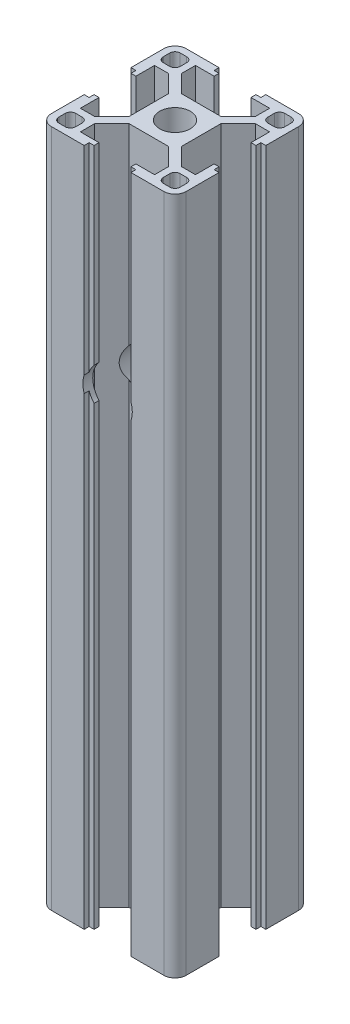
SolidWorks part; units mm, degrees
ref_plane "Front Plane" through (0, 0, 0) normal (0, 0, 1) x (1, 0, 0)
ref_plane "Top Plane" through (0, 0, 0) normal (0, 1, 0) x (1, 0, 0)
ref_plane "Right Plane" through (0, 0, 0) normal (1, 0, 0) x (0, 0, -1)
ref_plane "Plane1" through (0, 100, 0) normal (0, 1, 0) x (1, 0, 0)
sketch "Sketch1" plane through (0, 100, 0) normal (0, 1, 0) x (1, 0, 0)
  line L0 (28.5, -25.9) -> (28.5, -27.35)
  line L1 (27.35, -28.5) -> (25.9, -28.5)
  line L2 (24.75, -27.35) -> (24.75, -25.9)
  line L3 (25.9, -24.75) -> (27.35, -24.75)
  line L4 (1.5, -27.35) -> (1.5, -25.9)
  line L5 (2.65, -24.75) -> (4.1, -24.75)
  line L6 (5.25, -25.9) -> (5.25, -27.35)
  line L7 (4.1, -28.5) -> (2.65, -28.5)
  line L8 (2.65, -1.5) -> (4.1, -1.5)
  line L9 (5.25, -2.65) -> (5.25, -4.1)
  line L10 (4.1, -5.25) -> (2.65, -5.25)
  line L11 (1.5, -4.1) -> (1.5, -2.65)
  line L12 (28.5, -2.65) -> (28.5, -4.1)
  line L13 (27.35, -5.25) -> (25.9, -5.25)
  line L14 (24.75, -4.1) -> (24.75, -2.65)
  line L15 (25.9, -1.5) -> (27.35, -1.5)
  line L16 (27.5, 0) -> (20.2, 0)
  line L17 (20.2, 0) -> (20.2, -1.1)
  line L18 (20.2, -1.1) -> (19.1, -1.1)
  line L19 (19.1, -1.1) -> (19.1, -2.2)
  line L20 (19.1, -2.2) -> (23.25, -2.2)
  line L21 (23.25, -2.2) -> (23.25, -5.3358)
  line L22 (23.25, -5.3358) -> (19.3858, -9.2)
  line L23 (19.3858, -9.2) -> (10.6142, -9.2)
  line L24 (10.6142, -9.2) -> (6.75, -5.3358)
  line L25 (6.75, -5.3358) -> (6.75, -2.2)
  line L26 (6.75, -2.2) -> (10.9, -2.2)
  line L27 (10.9, -2.2) -> (10.9, -1.1)
  line L28 (10.9, -1.1) -> (9.8, -1.1)
  line L29 (9.8, -1.1) -> (9.8, 0)
  line L30 (9.8, 0) -> (2.5, 0)
  line L31 (0, -2.5) -> (0, -9.8)
  line L32 (0, -9.8) -> (1.1, -9.8)
  line L33 (1.1, -9.8) -> (1.1, -10.9)
  line L34 (1.1, -10.9) -> (2.2, -10.9)
  line L35 (2.2, -10.9) -> (2.2, -6.75)
  line L36 (2.2, -6.75) -> (5.3358, -6.75)
  line L37 (5.3358, -6.75) -> (9.2, -10.6142)
  line L38 (9.2, -10.6142) -> (9.2, -19.3858)
  line L39 (9.2, -19.3858) -> (5.3358, -23.25)
  line L40 (5.3358, -23.25) -> (2.2, -23.25)
  line L41 (2.2, -23.25) -> (2.2, -19.1)
  line L42 (2.2, -19.1) -> (1.1, -19.1)
  line L43 (1.1, -19.1) -> (1.1, -20.2)
  line L44 (1.1, -20.2) -> (0, -20.2)
  line L45 (0, -20.2) -> (0, -27.5)
  line L46 (2.5, -30) -> (9.8, -30)
  line L47 (9.8, -30) -> (9.8, -28.9)
  line L48 (9.8, -28.9) -> (10.9, -28.9)
  line L49 (10.9, -28.9) -> (10.9, -27.8)
  line L50 (10.9, -27.8) -> (6.75, -27.8)
  line L51 (6.75, -27.8) -> (6.75, -24.6642)
  line L52 (6.75, -24.6642) -> (10.6142, -20.8)
  line L53 (10.6142, -20.8) -> (19.3858, -20.8)
  line L54 (19.3858, -20.8) -> (23.25, -24.6642)
  line L55 (23.25, -24.6642) -> (23.25, -27.8)
  line L56 (23.25, -27.8) -> (19.1, -27.8)
  line L57 (19.1, -27.8) -> (19.1, -28.9)
  line L58 (19.1, -28.9) -> (20.2, -28.9)
  line L59 (20.2, -28.9) -> (20.2, -30)
  line L60 (20.2, -30) -> (27.5, -30)
  line L61 (30, -27.5) -> (30, -20.2)
  line L62 (30, -20.2) -> (28.9, -20.2)
  line L63 (28.9, -20.2) -> (28.9, -19.1)
  line L64 (28.9, -19.1) -> (27.8, -19.1)
  line L65 (27.8, -19.1) -> (27.8, -23.25)
  line L66 (27.8, -23.25) -> (24.6642, -23.25)
  line L67 (24.6642, -23.25) -> (20.8, -19.3858)
  line L68 (20.8, -19.3858) -> (20.8, -10.6142)
  line L69 (20.8, -10.6142) -> (24.6642, -6.75)
  line L70 (24.6642, -6.75) -> (27.8, -6.75)
  line L71 (27.8, -6.75) -> (27.8, -10.9)
  line L72 (27.8, -10.9) -> (28.9, -10.9)
  line L73 (28.9, -10.9) -> (28.9, -9.8)
  line L74 (28.9, -9.8) -> (30, -9.8)
  line L75 (30, -9.8) -> (30, -2.5)
  arc A0 (27.35, -24.75) -> (28.5, -25.9) centre (27.35, -25.9) cw
  arc A1 (28.5, -27.35) -> (27.35, -28.5) centre (27.35, -27.35) cw
  arc A2 (25.9, -28.5) -> (24.75, -27.35) centre (25.9, -27.35) cw
  arc A3 (24.75, -25.9) -> (25.9, -24.75) centre (25.9, -25.9) cw
  arc A4 (2.65, -28.5) -> (1.5, -27.35) centre (2.65, -27.35) cw
  arc A5 (1.5, -25.9) -> (2.65, -24.75) centre (2.65, -25.9) cw
  arc A6 (4.1, -24.75) -> (5.25, -25.9) centre (4.1, -25.9) cw
  arc A7 (5.25, -27.35) -> (4.1, -28.5) centre (4.1, -27.35) cw
  arc A8 (1.5, -2.65) -> (2.65, -1.5) centre (2.65, -2.65) cw
  arc A9 (4.1, -1.5) -> (5.25, -2.65) centre (4.1, -2.65) cw
  arc A10 (5.25, -4.1) -> (4.1, -5.25) centre (4.1, -4.1) cw
  arc A11 (2.65, -5.25) -> (1.5, -4.1) centre (2.65, -4.1) cw
  arc A12 (27.35, -1.5) -> (28.5, -2.65) centre (27.35, -2.65) cw
  arc A13 (28.5, -4.1) -> (27.35, -5.25) centre (27.35, -4.1) cw
  arc A14 (25.9, -5.25) -> (24.75, -4.1) centre (25.9, -4.1) cw
  arc A15 (24.75, -2.65) -> (25.9, -1.5) centre (25.9, -2.65) cw
  circle A16 centre (15, -15) radius 3.4
  arc A17 (30, -2.5) -> (27.5, 0) centre (27.5, -2.5) ccw
  arc A18 (2.5, 0) -> (0, -2.5) centre (2.5, -2.5) ccw
  arc A19 (0, -27.5) -> (2.5, -30) centre (2.5, -27.5) ccw
  arc A20 (27.5, -30) -> (30, -27.5) centre (27.5, -27.5) ccw
extrude "Boss-Extrude1" add sketch "Sketch1" against normal blind 151
sketch "Sketch2" plane through (0, 0, 20.8) normal (0, 0, 1) x (1, 0, 0)
  line L0 (15, 76.8101) -> (15, 31.1851) construction
  circle A0 centre (15, 76.8101) radius 3.125
  circle A1 centre (15, 53.9976) radius 5.5
  circle A2 centre (15, 31.1851) radius 3.125
  point P7 (15, 53.9976)
  dimension "D2" = 6.25
  dimension "D3" = 6.25
  dimension "D4" = 11
  dimension "D1" = 45.625
extrude "Cut-Extrude2" cut sketch "Sketch2" against normal through all both and the other way through all
